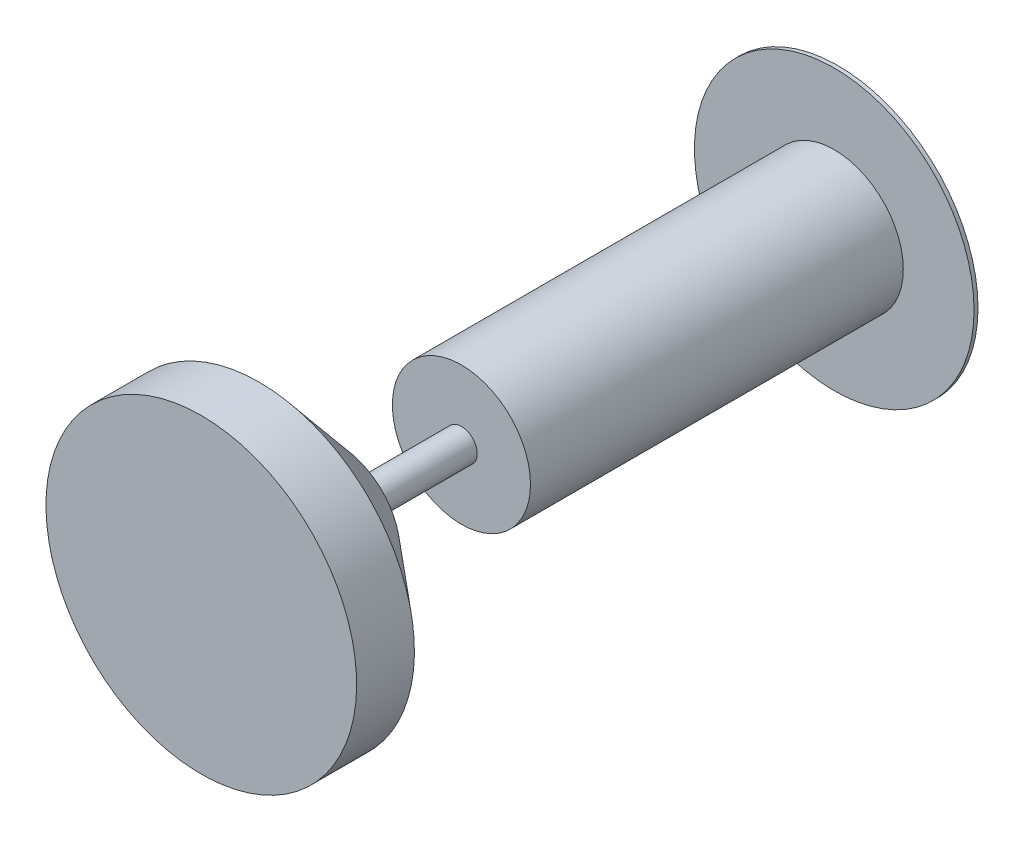
SolidWorks part; units mm, degrees
other "Markup1"
sketch "Sketch6" plane through (500, -500, -1363.6) normal (1, 0, 0) x (0, 0, -1)
ref_plane "Top Plane" through (0, 0, 0) normal (0, 0, 1) x (1, 0, 0)
ref_plane "Right Plane" through (0, 0, 0) normal (0, 1, 0) x (1, 0, 0)
ref_plane "Front Plane" through (0, 0, 0) normal (1, 0, 0) x (0, 0, -1)
sketch "Sketch1" plane through (0, 0, 0) normal (0, 0, 1) x (1, 0, 0)
  circle A0 centre (0, 0) radius 50.8
  dimension "D1" = 101.6
extrude "Boss-Extrude1" add sketch "Sketch1" against normal blind 1363.6 and the other way blind 686.4
sketch "Sketch2" plane through (0, 0, -1363.6) normal (0, 0, 1) x (1, 0, 0)
  circle A0 centre (0, 0) radius 450
  dimension "D1" = 900
extrude "Boss-Extrude2" add sketch "Sketch2" along normal blind 12.7
sketch "Sketch3" plane through (0, 0, -1350.9) normal (0, 0, 1) x (1, 0, 0)
  circle A0 centre (0, 0) radius 222.25
  dimension "D1" = 444.5
extrude "Boss-Extrude3" add sketch "Sketch3" along normal blind 1200
sketch "Sketch5" plane through (0, 0, 0) normal (1, 0, 0) x (0, 0, -1)
  line L0 (-686.4, 0) -> (-686.4, 500)
  line L1 (-686.4, 50.8) -> (-686.4, -50.8) construction
  line L2 (-686.4, 500) -> (-500.4, 500)
  line L3 (-500.4, 500) -> (-246.4, 200)
  line L4 (-246.4, 200) -> (-246.4, 0)
  line L5 (-246.4, 0) -> (-686.4, 0)
  dimension "D1" = 500
  dimension "D2" = 186
  dimension "D3" = 440
  dimension "D4" = 200
revolve "Revolve1" add sketch "Sketch5" angle 360 about L5
